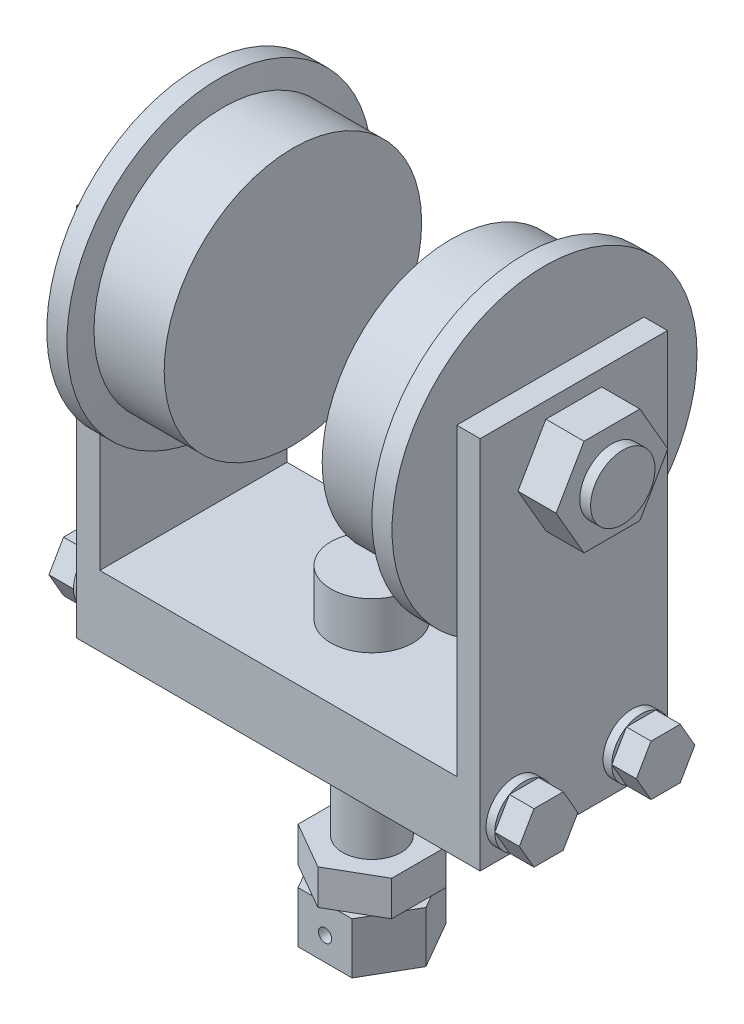
SolidWorks part; units mm, degrees
ref_plane "Front" through (0, 0, 0) normal (0, 0, 1) x (1, 0, 0)
ref_plane "Top" through (0, 0, 0) normal (0, 1, 0) x (1, 0, 0)
ref_plane "Right" through (0, 0, 0) normal (1, 0, 0) x (0, 0, -1)
ref_plane "Z PLANE" through (0, 0, 0) normal (0, 0, 1) x (1, 0, 0)
ref_plane "YOKE BOTTOM" through (0, 0, 0) normal (0, 1, 0) x (-1, 0, 0)
ref_plane "X PLANE" through (0, 0, 0) normal (1, 0, 0) x (0, 0, -1)
sketch "YOKE CROSS SECTION" plane through (0, 0, 0) normal (1, 0, 0) x (0, 0, -1)
  line L0 (0, 0) -> (0, 57.0916) construction
  line L1 (0, 84.8167) -> (0, -84.8167) construction
  line L2 (-50.8, 0) -> (50.8, 0)
  line L3 (69.1602, 0) -> (-69.1602, 0) construction
  line L4 (50.8, 0) -> (50.8, 38.1)
  line L5 (-50.8, 0) -> (-50.8, 38.1)
  line L6 (50.8, 38.1) -> (-50.8, 38.1)
  point P12 (0, 38.1)
  dimension "D1" = 38.1
  dimension "D2" = 101.6
ref_plane "1/2 YOKE LENGTH (A)" through (96.8375, 0, 0) normal (1, 0, 0) x (0, 0, -1)
extrude "YOKE" add sketch "YOKE CROSS SECTION" along normal up to surface (96.8375 mm away) up to plane "1/2 YOKE LENGTH (A)"
sketch "SIDEPLATE PROFILE" plane through (96.8375, 0, 0) normal (1, 0, 0) x (0, 0, -1)
  line L0 (0, 0) -> (0, 74.7424) construction
  line L1 (0, 84.8167) -> (0, -84.8167) construction
  line L2 (-50.8, 0) -> (50.8, 0)
  line L3 (50.8, 0) -> (50.8, 203.2)
  line L4 (-50.8, 0) -> (-50.8, 203.2)
  line L5 (50.8, 203.2) -> (-50.8, 203.2)
  point P11 (0, 203.2)
  dimension "D1" = 203.2
ref_plane "WHEEL HEIGHT" through (0, 168.275, 0) normal (0, 1, 0) x (-1, 0, 0)
ref_plane "SCREW LOCATION X" through (0, 0, 31.75) normal (0, 0, 1) x (1, 0, 0)
ref_plane "SCREW LOCATION Y" through (0, 19.05, 0) normal (0, 1, 0) x (-1, 0, 0)
extrude "SIDEPLATE" add sketch "SIDEPLATE PROFILE" along normal blind 12.7
sketch "WHEEL PIN NUT PROFILE" plane through (109.5375, 0, 0) normal (1, 0, 0) x (0, 0, -1)
  line L0 (0, 84.8167) -> (0, -84.8167) construction
  line L1 (30.3017, 168.275) -> (15.1508, 194.517)
  line L2 (15.1508, 194.517) -> (-15.1508, 194.517)
  line L3 (-15.1508, 194.517) -> (-30.3017, 168.275)
  line L4 (-30.3017, 168.275) -> (-15.1508, 142.033)
  line L5 (-15.1508, 142.033) -> (15.1508, 142.033)
  line L6 (15.1508, 142.033) -> (30.3017, 168.275)
  line L7 (69.1602, 168.275) -> (-69.1602, 168.275) construction
  circle A0 centre (0, 168.275) radius 26.242 construction
  dimension "D1" = 52.484
extrude "WHEEL PIN NUT" add sketch "WHEEL PIN NUT PROFILE" along normal blind 20.7061
sketch "WHEEL PIN PROJECTION PROFILE" plane through (130.2436, 0, 0) normal (1, 0, 0) x (0, 0, -1)
  line L0 (0, 84.8167) -> (0, -84.8167) construction
  line L1 (69.1602, 168.275) -> (-69.1602, 168.275) construction
  circle A0 centre (0, 168.275) radius 17.4625
  dimension "D1" = 34.925
extrude "WHEEL PIN PROJECTION" add sketch "WHEEL PIN PROJECTION PROFILE" along normal blind 5.8826
sketch "LOCKNUTS PROFILE" plane through (109.5375, 0, 0) normal (1, 0, 0) x (0, 0, -1)
  line L0 (-31.75, 84.8167) -> (-31.75, -84.8167) construction
  line L1 (50, 19.05) -> (-50, 19.05) construction
  circle A0 centre (-31.75, 19.05) radius 15.875
  dimension "D1" = 31.75
extrude "LOCKNUTS" add sketch "LOCKNUTS PROFILE" along normal blind 4.7625
sketch "SCREWS PROFILE" plane through (114.3, 0, 0) normal (1, 0, 0) x (0, 0, -1)
  line L0 (50, 19.05) -> (-50, 19.05) construction
  line L1 (-15.8755, 19.05) -> (-23.8127, 32.7978)
  line L2 (-23.8127, 32.7978) -> (-39.6873, 32.7978)
  line L3 (-39.6873, 32.7978) -> (-47.6245, 19.05)
  line L4 (-47.6245, 19.05) -> (-39.6873, 5.3023)
  line L5 (-39.6873, 5.3023) -> (-23.8127, 5.3023)
  line L6 (-23.8127, 5.3023) -> (-15.8755, 19.05)
  line L7 (-31.75, 84.8167) -> (-31.75, -84.8167) construction
  circle A0 centre (-31.75, 19.05) radius 13.7477 construction
  dimension "D1" = 27.4955
extrude "SCREWS" add sketch "SCREWS PROFILE" along normal blind 13.3223
sketch "PROFILE" plane through (0, 38.1, 0) normal (0, 1, 0) x (-1, 0, 0)
  line L0 (84.8167, 0) -> (-84.8167, 0) construction
  line L1 (0, 83.2389) -> (0, -83.2389) construction
  circle A0 centre (0, 0) radius 22.225
  dimension "D1" = 44.45
extrude "KING BOLT HEAD" add sketch "PROFILE" along normal blind 25.4
mirror "Mirror1" about plane through (0, 0, 0) normal (0, 0, 1) of "SCREWS", "LOCKNUTS"
mirror "Mirror5" about plane through (0, 0, 0) normal (1, 0, 0) of bodies 112
ref_plane "TOP OF NUT" through (0, -63.5, 0) normal (0, 1, 0) x (-1, 0, 0)
sketch "DIA." plane through (0, 0, 0) normal (0, -1, 0) x (1, 0, 0)
  line L0 (84.8167, 0) -> (-84.8167, 0) construction
  line L1 (0, -83.2389) -> (0, 83.2389) construction
  circle A0 centre (0, 0) radius 15.875
  dimension "D1" = 31.75
extrude "KING BOLT" add sketch "DIA." along normal up to surface (63.5 mm away) up to plane "TOP OF NUT"
sketch "KING BOLT JAN NUT PROFILE" plane through (0, -63.5, 0) normal (0, -1, 0) x (1, 0, 0)
  line L0 (84.8167, 0) -> (-84.8167, 0) construction
  line L1 (0, -29.3294) -> (25.4, -14.6647)
  line L2 (25.4, -14.6647) -> (25.4, 14.6647)
  line L3 (25.4, 14.6647) -> (0, 29.3294)
  line L4 (0, 29.3294) -> (-25.4, 14.6647)
  line L5 (-25.4, 14.6647) -> (-25.4, -14.6647)
  line L6 (-25.4, -14.6647) -> (0, -29.3294)
  line L7 (0, -83.2389) -> (0, 83.2389) construction
  circle A0 centre (0, 0) radius 25.4 construction
  dimension "D1" = 50.8
extrude "KING BOLT JAM NUT" add sketch "KING BOLT JAN NUT PROFILE" along normal blind 19.0754
sketch "KING BOLT NUT PROFILE" plane through (0, -82.5754, 0) normal (0, -1, 0) x (1, 0, 0)
  line L1 (29.3294, 0) -> (14.6647, 25.4)
  line L2 (14.6647, 25.4) -> (-14.6647, 25.4)
  line L3 (-14.6647, 25.4) -> (-29.3294, 0)
  line L4 (-29.3294, 0) -> (-14.6647, -25.4)
  line L5 (-14.6647, -25.4) -> (14.6647, -25.4)
  line L6 (14.6647, -25.4) -> (29.3294, 0)
  line L10 (0, -83.2389) -> (0, 83.2389) construction
  line L11 (84.8167, 0) -> (-84.8167, 0) construction
  circle A0 centre (0, 0) radius 25.4 construction
  dimension "D1" = 50.8
extrude "KING BOLT NUT" add sketch "KING BOLT NUT PROFILE" along normal blind 27.8003
sketch "Sketch5" plane through (0, -110.3757, 0) normal (0, -1, 0) x (1, 0, 0)
  circle A0 centre (0, 0) radius 15.875 construction
  circle A1 centre (0, 0) radius 15.875
extrude "EXTENDED KING BOLT" add sketch "Sketch5" along normal blind 6.35
chamfer "Chamfer1" distance 2.3812 angle 45 1 edges at (0, -116.7257, -15.875)
ref_plane "MOUNTING REF PLANE" through (0, -34.925, 0) normal (0, 1, 0) x (-1, 0, 0)
sketch "Sketch6" plane through (0, 0, 0) normal (0, 0, 1) x (1, 0, 0)
  line L0 (96.8375, 168.275) -> (42.8625, 168.275)
  line L1 (42.8625, 238.125) -> (42.8625, 168.275)
  line L2 (93.6625, 251.0244) -> (93.6625, 193.675)
  line L3 (96.8375, 168.275) -> (96.8375, 193.675)
  line L4 (96.8375, 193.675) -> (93.6625, 193.675)
  line L5 (80.9625, 238.125) -> (82.7474, 251.0244)
  line L6 (93.6625, 251.0244) -> (82.7474, 251.0244)
  line L7 (69.1602, 168.275) -> (-69.1602, 168.275) construction
  line L8 (80.9625, 238.125) -> (42.8625, 238.125)
  line L10 (96.8375, -75.0522) -> (96.8375, 75.0522) construction
  dimension "D2" = 69.85
  dimension "D1" = 3.175
  dimension "D3" = 50.8
  dimension "D5" = 25.4
  dimension "D6" = 82.7494
  dimension "D8" = 14.0901
  dimension "D9" = 15.875
revolve "WHEEL" add sketch "Sketch6" angle 360 about L0
mirror "Mirror6" about plane through (0, 0, 0) normal (1, 0, 0) of "WHEEL"
sketch "Sketch7" plane through (0, 0, 25.4) normal (0, 0, 1) x (1, 0, 0)
  line L0 (0, -83.2389) -> (0, 83.2389) construction
  line L1 (-14.6647, -110.3757) -> (-29.3294, -110.3757) construction
  circle A0 centre (0, -97.6757) radius 3.5719
  dimension "D2" = 7.1437
  dimension "D1" = 12.7
extrude "COTTER PIN HOLE" cut sketch "Sketch7" against normal up to next
sketch "Sketch8" plane through (0, 0, 0) normal (0, -1, 0) x (1, 0, 0)
  circle A0 centre (0, 0) radius 25.4
  circle A1 centre (0, 0) radius 30.1625
  dimension "D1" = 50.8
  dimension "D2" = 60.325
extrude "SPACER" [suppressed] add sketch "Sketch8" along normal blind 12.7
ref_plane "TREAD OF TRACK" through (0, 98.425, 0) normal (0, 1, 0) x (-1, 0, 0)
